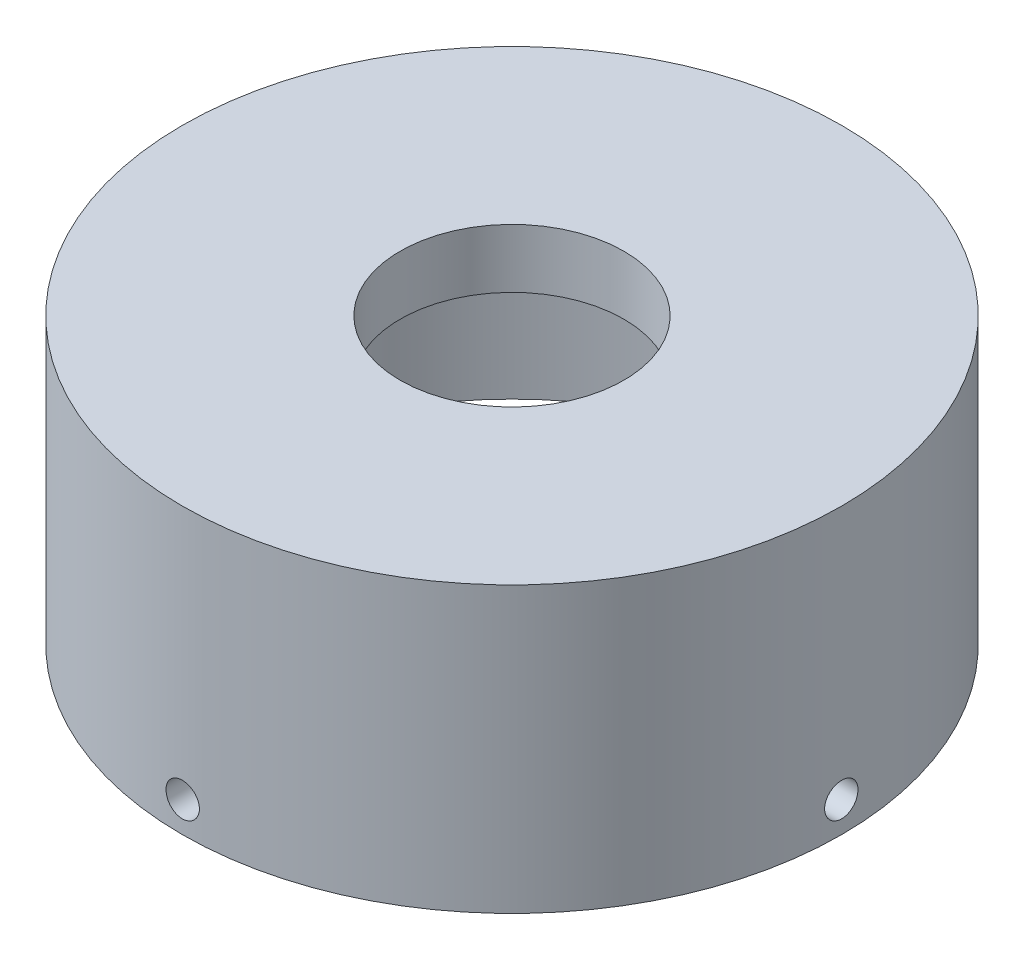
SolidWorks part; units mm, degrees
ref_plane "Front Plane" through (0, 0, 0) normal (0, 0, 1) x (1, 0, 0)
ref_plane "Top Plane" through (0, 0, 0) normal (0, 1, 0) x (1, 0, 0)
ref_plane "Right Plane" through (0, 0, 0) normal (1, 0, 0) x (0, 0, -1)
sketch "Sketch1" plane through (0, 0, 0) normal (0, 1, 0) x (1, 0, 0)
  circle A0 centre (0, 0) radius 38.1 construction
  circle A1 centre (0, 0) radius 38.862
  circle A2 centre (0, 0) radius 42.672
  dimension "D1" = 76.2
  dimension "D2" = 0.762
  dimension "D3" = 3.81
extrude "Boss-Extrude1" add sketch "Sketch1" along normal blind 29.21
sketch "Sketch2" plane through (0, 29.21, 0) normal (0, 1, 0) x (1, 0, 0)
  circle A0 centre (0, 0) radius 42.672
  circle A1 centre (0, 0) radius 14.478
  circle A2 centre (0, 0) radius 42.672 construction
  dimension "D1" = 28.956
extrude "Boss-Extrude2" add sketch "Sketch2" along normal blind 7.62
sketch "Sketch3" plane through (0, 0, 0) normal (0, 0, 1) x (1, 0, 0)
  line L1 (-42.672, 0) -> (42.672, 0) construction
  circle A0 centre (0, 3.937) radius 2.159
  dimension "D1" = 4.318
  dimension "D2" = 1.778
extrude "Cut-Extrude1" cut sketch "Sketch3" against normal through all both and the other way through all
pattern_circular "CirPattern1" count 4 over 360 about axis through (0, 29.21, 0) along (0, -1, 0) of "Cut-Extrude1"
